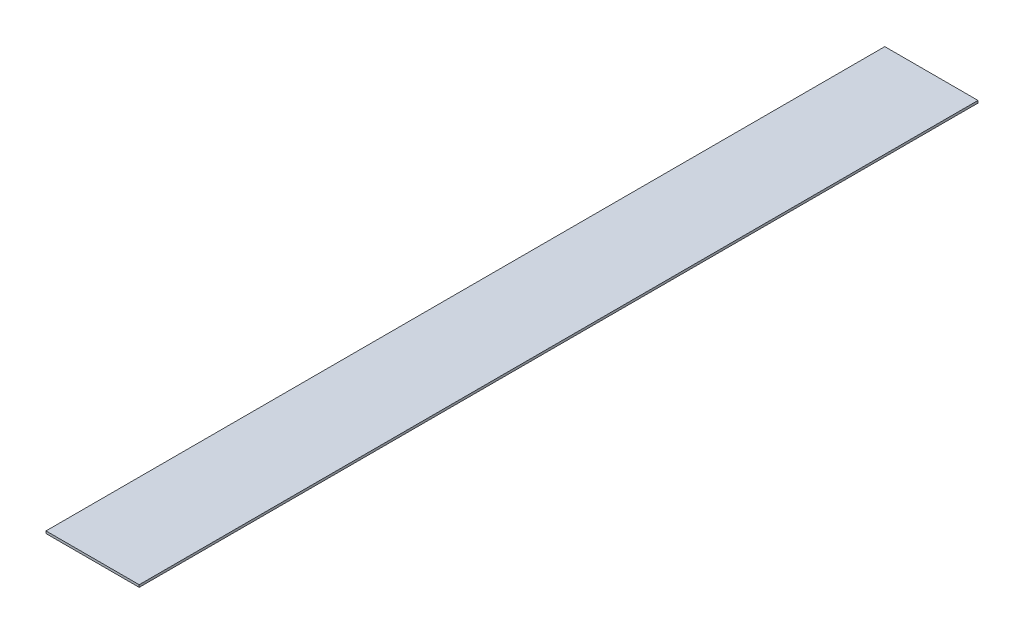
SolidWorks part; units mm, degrees
ref_plane "Front Plane" through (0, 0, 0) normal (0, 0, 1) x (1, 0, 0)
ref_plane "Top Plane" through (0, 0, 0) normal (0, 1, 0) x (1, 0, 0)
ref_plane "Right Plane" through (0, 0, 0) normal (1, 0, 0) x (0, 0, -1)
sketch "Sketch1" plane through (0, 0, 0) normal (0, 1, 0) x (1, 0, 0)
  line L1 (-25.4, -228.6) -> (25.4, -228.6)
  line L2 (-25.4, -228.6) -> (-25.4, 228.6)
  line L3 (-25.4, 228.6) -> (25.4, 228.6)
  line L4 (25.4, -228.6) -> (25.4, 228.6)
  line L5 (-25.4, -228.6) -> (25.4, 228.6) construction
  line L6 (-25.4, 228.6) -> (25.4, -228.6) construction
  point P0 (0, 0)
  dimension "D1" = 50.8
  dimension "D2" = 457.2
extrude "Boss-Extrude1" add sketch "Sketch1" along normal blind 1.27
